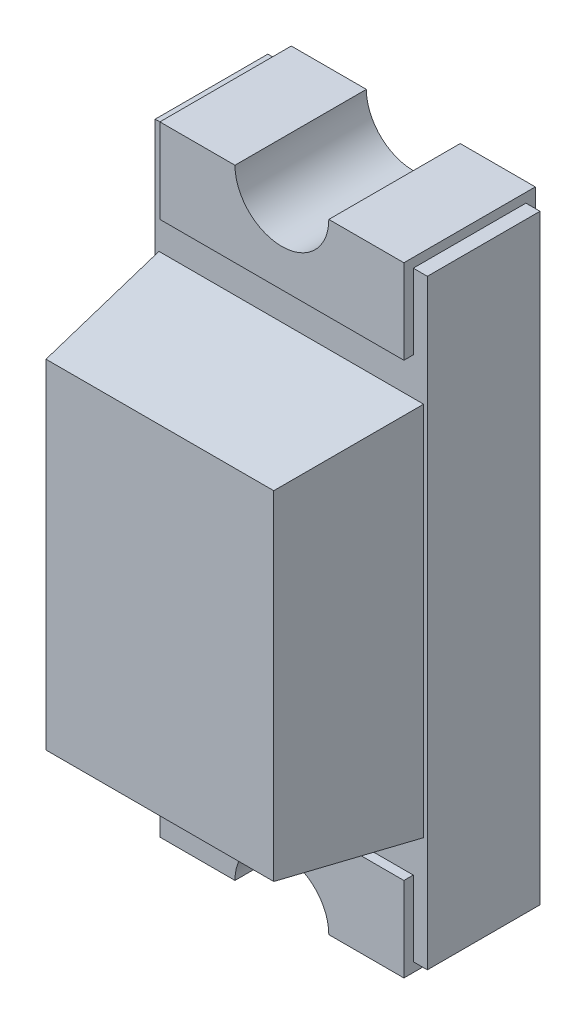
SolidWorks part; units mm, degrees
ref_plane "Front Plane" through (0, 0, 0) normal (0, 0, 1) x (1, 0, 0)
ref_plane "Top Plane" through (0, 0, 0) normal (0, 1, 0) x (1, 0, 0)
ref_plane "Right Plane" through (0, 0, 0) normal (1, 0, 0) x (0, 0, -1)
sketch "Esboço1" plane through (0, 0, 0) normal (0, 0, 1) x (1, 0, 0)
  line L1 (0.8736, 0.2076) -> (1.0736, 0.2076)
  line L2 (0.8736, 0.2076) -> (0.8736, -0.0174)
  line L3 (0.8736, -0.0174) -> (1.5236, -0.0174)
  line L4 (1.5236, 0.2076) -> (1.5236, -0.0174)
  line L5 (0.8736, -1.2174) -> (1.5236, -1.2174)
  line L6 (0.8736, -1.2174) -> (0.8736, -1.4424)
  line L7 (0.8736, -1.4424) -> (1.0736, -1.4424)
  line L8 (1.5236, -1.2174) -> (1.5236, -1.4424)
  line L9 (1.3236, 0.2076) -> (1.5236, 0.2076)
  line L10 (1.3236, -1.4424) -> (1.5236, -1.4424)
  arc A1 (1.0736, 0.2076) -> (1.3236, 0.2076) centre (1.1986, 0.2076) ccw
  arc A2 (1.3236, -1.4424) -> (1.0736, -1.4424) centre (1.1986, -1.4424) ccw
  dimension "D7" = 0.25
  dimension "D1" = 0.65
  dimension "D2" = 0.225
  dimension "D3" = 0.65
  dimension "D4" = 0.225
  dimension "D5" = 0
  dimension "D6" = 1.2
extrude "Ressalto-extrusão1" add sketch "Esboço1" along normal blind 0.35 separate body
sketch "Esboço2" plane through (0, 0, 0) normal (0, 0, 1) x (1, 0, 0)
  line L0 (0.8736, -0.0174) -> (1.5236, -0.0174) construction
  line L1 (0.8361, 0.1826) -> (1.0236, 0.1826)
  line L2 (0.8361, 0.1826) -> (0.8361, -1.4174)
  line L3 (0.8361, -1.4174) -> (1.0236, -1.4174)
  line L4 (1.5611, 0.1826) -> (1.5611, -1.4174)
  line L6 (1.3736, -1.4174) -> (1.5611, -1.4174)
  line L7 (1.3736, 0.1826) -> (1.5611, 0.1826)
  arc A0 (1.0736, 0.2076) -> (1.3236, 0.2076) centre (1.1986, 0.2076) ccw construction
  arc A1 (1.0236, 0.1826) -> (1.3736, 0.1826) centre (1.1986, 0.1826) ccw
  arc A2 (1.3736, -1.4174) -> (1.0236, -1.4174) centre (1.1986, -1.4174) ccw
  dimension "D5" = 0.35
  dimension "D1" = 0.725
  dimension "D2" = 1.6
  dimension "D3" = 0.2
  dimension "D4" = 0.3625
extrude "Ressalto-extrusão2" add sketch "Esboço2" along normal blind 0.3 from offset 0.025
sketch "Esboço3" plane through (0, 0, 0.325) normal (0, 0, 1) x (1, 0, 0)
  line L1 (1.5611, -1.4174) -> (1.5611, 0.1826) construction
  line L2 (0.8461, -0.1174) -> (1.5511, -0.1174)
  line L3 (0.8461, -0.1174) -> (0.8461, -1.1174)
  line L4 (0.8461, -1.1174) -> (1.5511, -1.1174)
  line L6 (1.5511, -0.1174) -> (1.5511, -1.1174)
  point P4 (1.5611, -0.6174)
  dimension "D1" = 0.5
  dimension "D2" = 1
  dimension "D3" = 0.705
  dimension "D4" = 0.01
extrude "Ressalto-extrusão3" add sketch "Esboço3" along normal blind 0.35 draft 8
